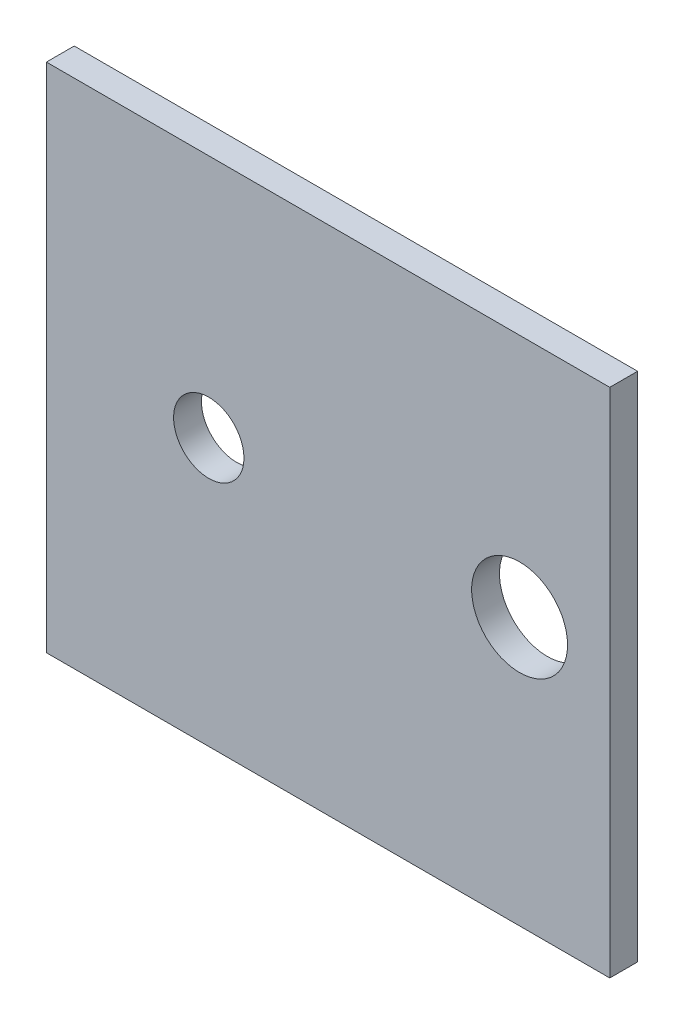
SolidWorks part; units mm, degrees
ref_plane "Alzado" through (0, 0, 0) normal (0, 0, 1) x (1, 0, 0)
ref_plane "Planta" through (0, 0, 0) normal (0, 1, 0) x (1, 0, 0)
ref_plane "Vista lateral" through (0, 0, 0) normal (1, 0, 0) x (0, 0, -1)
sketch "Croquis1" plane through (0, 0, 0) normal (0, 0, 1) x (1, 0, 0)
  line L1 (-54.8277, 48.1512) -> (33.2723, 48.1512)
  line L2 (-54.8277, 48.1512) -> (-54.8277, -31.8488)
  line L3 (-54.8277, -31.8488) -> (33.2723, -31.8488)
  line L4 (33.2723, 48.1512) -> (33.2723, -31.8488)
  dimension "D1" = 80
  dimension "D2" = 88.1
extrude "Saliente-Extruir1" add sketch "Croquis1" along normal blind 4.35
sketch "Croquis2" plane through (0, 0, 4.35) normal (0, 0, 1) x (1, 0, 0)
  line L1 (-54.8277, -31.8488) -> (33.2723, -31.8488) construction
  line L2 (33.2723, -31.8488) -> (33.2723, 48.1512) construction
  line L3 (-54.8277, 48.1512) -> (-54.8277, -31.8488) construction
  circle A0 centre (19.1723, 9.9612) radius 7.5
  circle A1 centre (-29.4377, 9.9612) radius 5.5
  dimension "D1" = 15
  dimension "D4" = 11
  dimension "D2" = 14.1
  dimension "D3" = 41.81
  dimension "D5" = 25.39
  dimension "D6" = 41.81
extrude "Cortar-Extruir1" cut sketch "Croquis2" against normal through all
